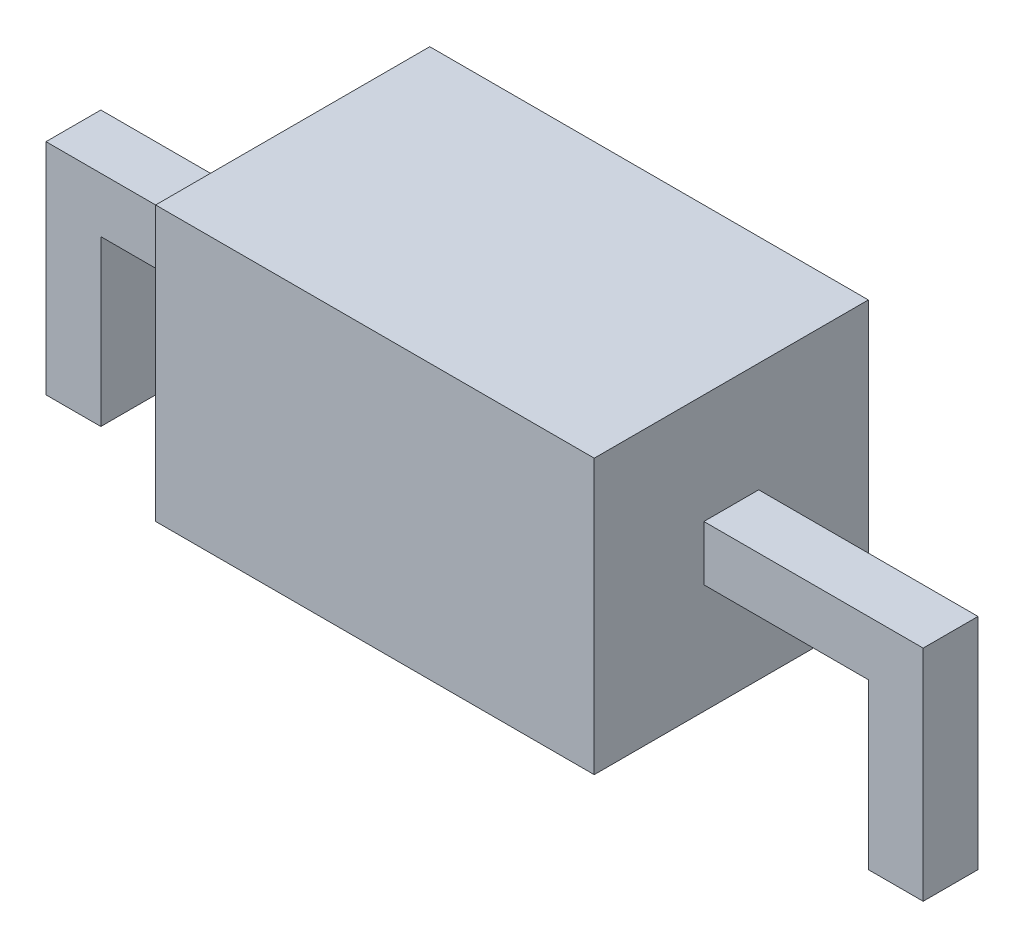
SolidWorks part; units mm, degrees
ref_plane "Front Plane" through (0, 0, 0) normal (0, 0, 1) x (1, 0, 0)
ref_plane "Top Plane" through (0, 0, 0) normal (0, 1, 0) x (1, 0, 0)
ref_plane "Right Plane" through (0, 0, 0) normal (1, 0, 0) x (0, 0, -1)
sketch "Sketch3" plane through (0, 0, 0) normal (0, 0, 1) x (1, 0, 0)
  line L1 (-2, 1.25) -> (2, 1.25)
  line L2 (-2, 1.25) -> (-2, -1.25)
  line L3 (-2, -1.25) -> (2, -1.25)
  line L4 (2, 1.25) -> (2, -1.25)
  line L5 (-2, 1.25) -> (2, -1.25) construction
  line L6 (-2, -1.25) -> (2, 1.25) construction
  point P0 (0, 0)
  dimension "D1" = 4
  dimension "D2" = 2.5
extrude "Boss-Extrude1" add sketch "Sketch3" along normal blind 2.5
ref_plane "Plane1" through (0, 0, 1.25) normal (0, 0, 1) x (1, 0, 0)
sketch "Sketch6" plane through (0, 0, 1.25) normal (0, 0, 1) x (1, 0, 0)
  line L0 (2, 0.25) -> (2, -0.25)
  line L1 (2, -1.25) -> (2, 1.25) construction
  line L2 (2, 0.25) -> (4, 0.25)
  line L3 (4, 0.25) -> (4, -0.25)
  line L4 (4, -0.25) -> (2, -0.25)
  line L5 (3.5, 0.25) -> (3.5, -1.75)
  line L6 (3.5, -1.75) -> (4, -1.75)
  line L7 (4, -1.75) -> (4, -0.25)
  line L8 (0, 0) -> (0, 1.1987)
  line L9 (-3.5, -1.75) -> (-4, -1.75)
  line L10 (-4, -1.75) -> (-4, -0.25)
  line L11 (-4, 0.25) -> (-4, -0.25)
  line L12 (-3.5, 0.25) -> (-3.5, -1.75)
  line L13 (-4, -0.25) -> (-2, -0.25)
  line L14 (-2, 0.25) -> (-2, -0.25)
  line L15 (-2, 0.25) -> (-4, 0.25)
  point P5 (2, 0)
  dimension "D1" = 0.5
  dimension "D2" = 2
  dimension "D3" = 2
  dimension "D4" = 0.5
extrude "Boss-Extrude2" add sketch "Sketch6" along normal blind 0.25 and the other way blind 0.25 contours L5 L2 L0 L4 | L2 L5 L4 L3 | L6 L7 L4 L5 | L14 L15 L12 L13 | L12 L15 L11 L13 | L13 L10 L9 L12
